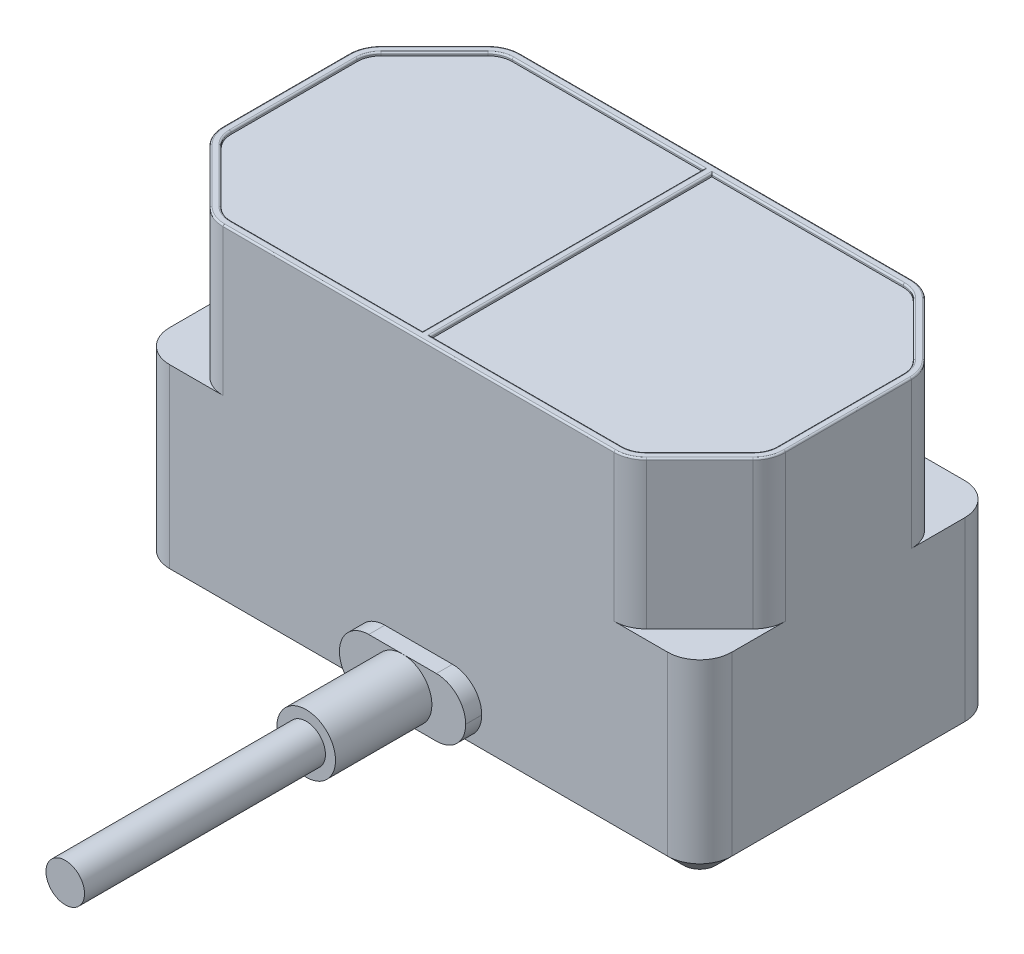
SolidWorks part; units mm, degrees
ref_plane "前视基准面" through (0, 0, 0) normal (0, 0, 1) x (1, 0, 0)
ref_plane "上视基准面" through (0, 0, 0) normal (0, 1, 0) x (1, 0, 0)
ref_plane "右视基准面" through (0, 0, 0) normal (1, 0, 0) x (0, 0, -1)
sketch "草图1" plane through (0, 0, 0) normal (0, 1, 0) x (1, 0, 0)
  line L1 (-17.5, -9.25) -> (17.5, -9.25)
  line L2 (-17.5, -9.25) -> (-17.5, 9.25)
  line L3 (-17.5, 9.25) -> (17.5, 9.25)
  line L4 (17.5, -9.25) -> (17.5, 9.25)
  line L5 (-17.5, -9.25) -> (17.5, 9.25) construction
  line L6 (-17.5, 9.25) -> (17.5, -9.25) construction
  point P0 (0, 0)
  dimension "D1" = 35
  dimension "D2" = 18.5
extrude "凸台-拉伸1" add sketch "草图1" along normal blind 12
sketch "草图2" plane through (0, 12, 0) normal (0, 1, 0) x (1, 0, 0)
  line L0 (-13, 9.25) -> (-17.5, 4.75)
  line L1 (17.5, 9.25) -> (-17.5, 9.25) construction
  line L2 (-17.5, 9.25) -> (-17.5, -9.25) construction
  line L3 (-17.5, 4.75) -> (-17.5, -4.75)
  line L4 (-17.5, -4.75) -> (-13, -9.25)
  line L5 (-17.5, -9.25) -> (17.5, -9.25) construction
  line L6 (-13, -9.25) -> (13, -9.25)
  line L7 (13, -9.25) -> (17.5, -4.75)
  line L8 (17.5, -9.25) -> (17.5, 9.25) construction
  line L9 (17.5, -4.75) -> (17.5, 4.75)
  line L10 (17.5, 4.75) -> (13, 9.25)
  line L11 (13, 9.25) -> (-13, 9.25)
  dimension "D1" = 4.5
  dimension "D2" = 4.5
  dimension "D3" = 4.5
  dimension "D4" = 4.5
  dimension "D5" = 4.5
extrude "凸台-拉伸2" add sketch "草图2" along normal blind 9
fillet "圆角1" radius 2 12 edges at (-13, 16.5, -9.25) (-17.5, 16.5, -4.75) (13, 16.5, -9.25) (17.5, 16.5, -4.75) (17.5, 16.5, 4.75) (13, 16.5, 9.25) (-17.5, 16.5, 4.75) (-13, 16.5, 9.25) (17.5, 6, 9.25) (17.5, 6, -9.25) (-17.5, 6, -9.25) (-17.5, 6, 9.25)
chamfer "倒角1" distance 1 angle 45 8 edges at (16.9142, 0, -8.6642) (0, 0, -9.25) (-16.9142, 0, -8.6642) (-17.5, 0, 0) (-16.9142, 0, 8.6642) (0, 0, 9.25) (16.9142, 0, 8.6642) (17.5, 0, 0)
sketch "草图3" plane through (0, 0, 9.25) normal (0, 0, 1) x (1, 0, 0)
  line L0 (-15.5, 1) -> (15.5, 1) construction
  line L1 (-2.106, 1) -> (2.106, 1)
  line L2 (-3.93, 2.824) -> (-3.93, 2.826)
  line L3 (-2.106, 4.65) -> (2.106, 4.65)
  line L4 (3.93, 2.824) -> (3.93, 2.826)
  line L5 (-3.93, 1) -> (3.93, 4.65) construction
  line L6 (-3.93, 4.65) -> (3.93, 1) construction
  arc A0 (2.106, 1) -> (3.93, 2.824) centre (2.106, 2.824) ccw
  arc A1 (2.106, 4.65) -> (3.93, 2.826) centre (2.106, 2.826) cw
  arc A2 (-2.106, 1) -> (-3.93, 2.824) centre (-2.106, 2.824) cw
  arc A3 (-3.93, 2.826) -> (-2.106, 4.65) centre (-2.106, 2.826) cw
  point P0 (0, 2.825)
  dimension "D4" = 1.824
  dimension "D1" = 3.65
  dimension "D2" = 7.86
  dimension "D3" = 0
extrude "凸台-拉伸3" add sketch "草图3" along normal blind 1
sketch "草图4" plane through (0, 0, 10.25) normal (0, 0, 1) x (1, 0, 0)
  line L0 (0, 1) -> (0, 4.65) construction
  line L1 (-2.106, 1) -> (2.106, 1) construction
  line L2 (2.106, 4.65) -> (-2.106, 4.65) construction
  line L3 (-3.93, 2.826) -> (3.93, 2.824) construction
  circle A0 centre (0, 2.825) radius 1.825
extrude "凸台-拉伸4" add sketch "草图4" along normal blind 6
sketch "草图5" plane through (0, 0, 16.25) normal (0, 0, 1) x (1, 0, 0)
  circle A0 centre (0, 2.825) radius 1.2
  dimension "D1" = 2.4
extrude "凸台-拉伸5" add sketch "草图5" along normal blind 15
sketch "草图6" plane through (0, 0, 0) normal (0, -1, 0) x (1, 0, 0)
  line L1 (-14, -5.75) -> (14, -5.75) construction
  line L2 (-14, -5.75) -> (-14, 5.75) construction
  line L3 (-14, 5.75) -> (14, 5.75) construction
  line L4 (14, -5.75) -> (14, 5.75) construction
  line L5 (-14, -5.75) -> (14, 5.75) construction
  line L6 (-14, 5.75) -> (14, -5.75) construction
  circle A0 centre (-14, 5.75) radius 1
  circle A1 centre (14, -5.75) radius 1
  point P0 (0, 0)
  dimension "D3" = 2
  dimension "D4" = 2
  dimension "D1" = 28
  dimension "D2" = 11.5
extrude "切除-拉伸1" cut sketch "草图6" against normal blind 4
fillet "圆角2" radius 0.3 2 edges at (14, 0, -6.75) (-14, 0, 4.75)
sketch "草图7" plane through (0, 21, 0) normal (0, 1, 0) x (1, 0, 0)
  line L0 (-16.9142, 5.3358) -> (-13.5858, 8.6642)
  line L1 (-12.1716, 9.25) -> (12.1716, 9.25)
  line L2 (-17.5, 3.9216) -> (-17.5, -3.9216)
  line L3 (-12.1716, -9.25) -> (12.1716, -9.25)
  line L4 (17.5, 3.9216) -> (17.5, -3.9216)
  line L5 (13.5858, 8.6642) -> (16.9142, 5.3358)
  line L6 (16.9142, -5.3358) -> (13.5858, -8.6642)
  line L7 (-16.9142, -5.3358) -> (-13.5858, -8.6642)
  line L8 (-16.5607, 4.9822) -> (-13.2322, 8.3107)
  line L9 (-12.1716, 8.75) -> (-0.25, 8.75)
  line L10 (13.2322, 8.3107) -> (16.5607, 4.9822)
  line L11 (17, 3.9216) -> (17, -3.9216)
  line L12 (16.5607, -4.9822) -> (13.2322, -8.3107)
  line L13 (-12.1716, -8.75) -> (-0.25, -8.75)
  line L14 (-16.5607, -4.9822) -> (-13.2322, -8.3107)
  line L15 (-17, 3.9216) -> (-17, -3.9216)
  line L16 (0.25, 8.75) -> (12.1716, 8.75)
  line L17 (-0.25, 8.75) -> (-0.25, -8.75)
  line L18 (0.25, 8.75) -> (0.25, -8.75)
  line L19 (0.25, -8.75) -> (12.1716, -8.75)
  line L21 (-12.1716, -8.75) -> (12.1716, -8.75) construction
  line L22 (-12.1716, 8.75) -> (12.1716, 8.75) construction
  arc A0 (13.5858, 8.6642) -> (12.1716, 9.25) centre (12.1716, 7.25) ccw
  arc A1 (16.9142, 5.3358) -> (17.5, 3.9216) centre (15.5, 3.9216) cw
  arc A2 (16.9142, -5.3358) -> (17.5, -3.9216) centre (15.5, -3.9216) ccw
  arc A3 (13.5858, -8.6642) -> (12.1716, -9.25) centre (12.1716, -7.25) cw
  arc A4 (-13.5858, -8.6642) -> (-12.1716, -9.25) centre (-12.1716, -7.25) ccw
  arc A5 (-16.9142, -5.3358) -> (-17.5, -3.9216) centre (-15.5, -3.9216) cw
  arc A6 (-16.9142, 5.3358) -> (-17.5, 3.9216) centre (-15.5, 3.9216) ccw
  arc A7 (-13.5858, 8.6642) -> (-12.1716, 9.25) centre (-12.1716, 7.25) cw
  arc A8 (-13.2322, 8.3107) -> (-12.1716, 8.75) centre (-12.1716, 7.25) cw
  arc A9 (13.2322, 8.3107) -> (12.1716, 8.75) centre (12.1716, 7.25) ccw
  arc A10 (16.5607, 4.9822) -> (17, 3.9216) centre (15.5, 3.9216) cw
  arc A11 (16.5607, -4.9822) -> (17, -3.9216) centre (15.5, -3.9216) ccw
  arc A12 (13.2322, -8.3107) -> (12.1716, -8.75) centre (12.1716, -7.25) cw
  arc A13 (-13.2322, -8.3107) -> (-12.1716, -8.75) centre (-12.1716, -7.25) ccw
  arc A14 (-16.5607, -4.9822) -> (-17, -3.9216) centre (-15.5, -3.9216) cw
  arc A15 (-16.5607, 4.9822) -> (-17, 3.9216) centre (-15.5, 3.9216) ccw
  dimension "D1" = 2
  dimension "D2" = 0.5
extrude "凸台-拉伸6" add sketch "草图7" along normal blind 0.2
fillet "圆角3" radius 0.1 36 edges at (0.25, 21.2, 0) (6.2108, 21.2, 8.75) (12.7456, 21.2, 8.6358) (14.8964, 21.2, 6.6464) (16.8858, 21.2, 4.4956) (17, 21.2, 0) (16.8858, 21.2, -4.4956) (14.8964, 21.2, -6.6464) (12.7456, 21.2, -8.6358) (6.2108, 21.2, -8.75) (-16.8858, 21.2, 4.4956) (-14.8964, 21.2, 6.6464) (-12.7456, 21.2, 8.6358) (-6.2108, 21.2, 8.75) (-0.25, 21.2, 0) (-6.2108, 21.2, -8.75) (-12.7456, 21.2, -8.6358) (-14.8964, 21.2, -6.6464) (-16.8858, 21.2, -4.4956) (-17, 21.2, 0) (15.25, 21.2, -7) (17.3478, 21.2, -4.6869) (17.5, 21.2, 0) (17.3478, 21.2, 4.6869) (15.25, 21.2, 7) (12.9369, 21.2, 9.0978) (0, 21.2, 9.25) (-12.9369, 21.2, 9.0978) (-15.25, 21.2, 7) (-17.3478, 21.2, 4.6869) (-17.5, 21.2, 0) (-17.3478, 21.2, -4.6869) (-15.25, 21.2, -7) (-12.9369, 21.2, -9.0978) (0, 21.2, -9.25) (12.9369, 21.2, -9.0978)
